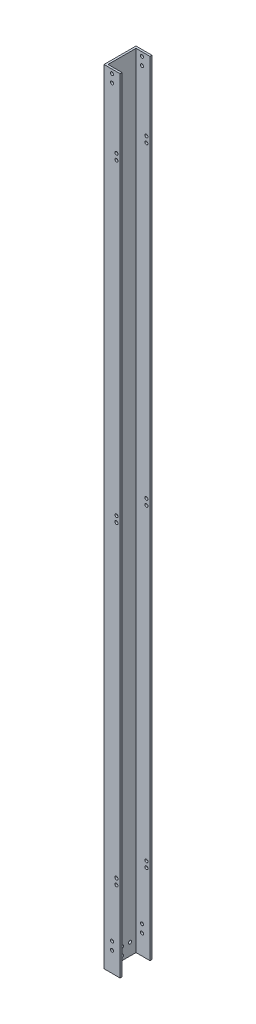
SolidWorks part; units mm, degrees
material "6061-T6 (SS)"
ref_plane "Front Plane" through (0, 0, 0) normal (0, 0, 1) x (1, 0, 0)
ref_plane "Top Plane" through (0, 0, 0) normal (0, 1, 0) x (1, 0, 0)
ref_plane "Right Plane" through (0, 0, 0) normal (1, 0, 0) x (0, 0, -1)
sketch "Sketch1" plane through (0, 0, 0) normal (0, 1, 0) x (1, 0, 0)
  line L1 (0, 0) -> (25.4, 0)
  line L2 (0, 0) -> (0, 50.8)
  line L3 (0, 50.8) -> (25.4, 50.8)
  line L4 (25.4, 0) -> (25.4, 50.8)
  dimension "D1" = 25.4
  dimension "D2" = 50.8
extrude "Extrude-Thin1" add sketch "Sketch1" along normal blind 1244.6 thin thin type one direction reverse wall 3.175
sketch "Sketch5" plane through (0, 1244.6, 0) normal (0, 1, 0) x (1, 0, 0)
  line L0 (22.225, 47.625) -> (25.4, 47.625)
  line L1 (25.4, 0) -> (25.4, 50.8) construction
  line L2 (22.225, 3.175) -> (25.4, 3.175)
  line L3 (25.4, 3.175) -> (25.4, 47.625)
  line L4 (22.225, 47.625) -> (22.225, 3.175)
extrude "Cut-Extrude2" cut sketch "Sketch5" against normal through all
sketch "Sketch6" plane through (0, 0, 0) normal (0, 0, 1) x (1, 0, 0)
  line L0 (25.4, 1244.6) -> (25.4, 0) construction
  line L1 (19.685, 1122.68) -> (20.32, 633.4125) construction
  line L2 (20.32, 623.8875) -> (19.685, 134.62) construction
  circle A0 centre (19.685, 1132.205) radius 2.4892 construction
  circle A1 centre (19.685, 1122.68) radius 2.4892 construction
  circle A4 centre (19.685, 125.095) radius 2.4892 construction
  circle A5 centre (19.685, 134.62) radius 2.4892 construction
  circle A6 centre (19.685, 1132.205) radius 2.4892
  circle A7 centre (19.685, 1122.68) radius 2.4892
  circle A8 centre (20.32, 633.4125) radius 2.4892
  circle A9 centre (20.32, 623.8875) radius 2.4892
  circle A10 centre (19.685, 125.095) radius 2.4892
  circle A11 centre (19.685, 134.62) radius 2.4892
  dimension "D3" = 4.9784
  dimension "D1" = 9.525
  dimension "D2" = 5.08
sketch "Sketch8" plane through (0, 0, 0) normal (-1, 0, 0) x (0, 0, 1)
  circle A0 centre (-25.4, 19.05) radius 2.4892 construction
  circle A1 centre (-25.4, 6.35) radius 2.4892 construction
  circle A2 centre (-25.4, 19.05) radius 2.4892
  circle A3 centre (-25.4, 6.35) radius 2.4892
  circle A4 centre (-38.1, 19.05) radius 2.4892 construction
  circle A5 centre (-12.7, 19.05) radius 2.4892 construction
  circle A6 centre (-38.1, 19.05) radius 2.4892
  circle A7 centre (-12.7, 19.05) radius 2.4892
extrude "Cut-Extrude4" cut sketch "Sketch8" against normal through all
sketch "Sketch9" plane through (0, 0, 0) normal (0, 0, 1) x (1, 0, 0)
  line L1 (0, 1244.6) -> (0, 0) construction
  line L2 (3.175, 50.8) -> (252.095, 50.8) construction
  line L3 (3.175, 25.4) -> (252.095, 25.4) construction
  line L5 (0, 1244.6) -> (25.4, 1244.6) construction
  line L6 (3.175, 1219.2) -> (252.095, 1219.2) construction
  circle A0 centre (12.7, 44.45) radius 2.4892
  circle A1 centre (12.7, 31.75) radius 2.4892
  circle A2 centre (12.7, 1238.25) radius 2.4892
  circle A3 centre (12.7, 1225.55) radius 2.4892
  dimension "D1" = 4.9784
  dimension "D5" = 4.9784
  dimension "D2" = 12.7
  dimension "D3" = 6.35
  dimension "D4" = 6.35
  dimension "D6" = 12.7
  dimension "D7" = 6.35
  dimension "D8" = 6.35
extrude "Cut-Extrude5" cut sketch "Sketch9" against normal through all
extrude "Cut-Extrude6" cut sketch "Sketch6" against normal through all both and the other way through all contours A6 | A11 | A10 | A7
sketch "Sketch10" plane through (0, 0, -50.8) normal (0, 0, -1) x (-1, 0, 0)
  line L0 (-19.685, 1122.68) -> (-19.685, 134.62) construction
  line L1 (-110.9513, 628.65) -> (71.5813, 628.65) construction
  circle A0 centre (-19.685, 633.4125) radius 2.4892
  circle A1 centre (-19.685, 623.8875) radius 2.4892
  point P6 (-19.685, 628.65)
  dimension "D1" = 4.9784
  dimension "D2" = 4.9784
  dimension "D3" = 9.525
  dimension "D4" = 4.7625
extrude "Cut-Extrude7" cut sketch "Sketch10" against normal through all
equation "\"D4@Sketch10\"=\"D3@Sketch10\"/2"
